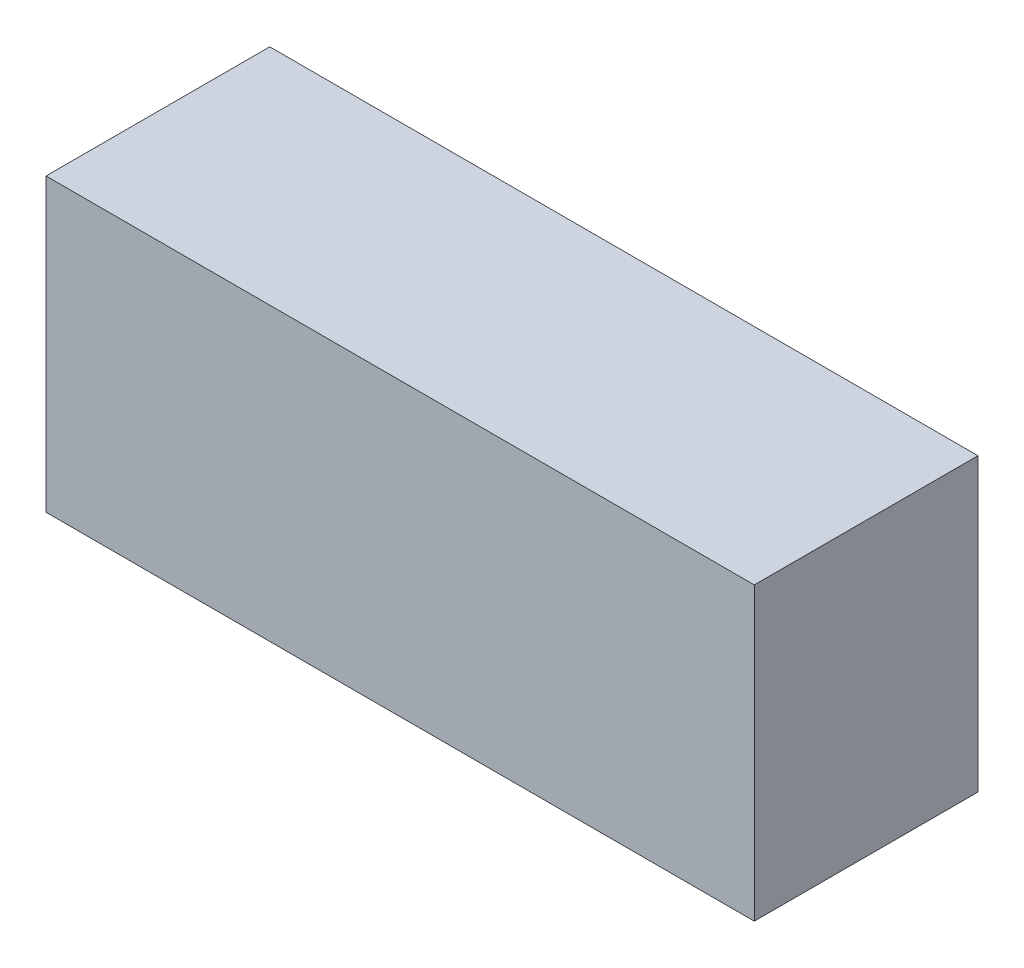
SolidWorks part; units mm, degrees
ref_plane "Front Plane" through (0, 0, 0) normal (0, 0, 1) x (1, 0, 0)
ref_plane "Top Plane" through (0, 0, 0) normal (0, 1, 0) x (1, 0, 0)
ref_plane "Right Plane" through (0, 0, 0) normal (1, 0, 0) x (0, 0, -1)
sketch "Sketch1" plane through (0, 0, 0) normal (0, 1, 0) x (1, 0, 0)
  line L1 (-67.945, 21.463) -> (67.945, 21.463)
  line L2 (-67.945, 21.463) -> (-67.945, -21.463)
  line L3 (-67.945, -21.463) -> (67.945, -21.463)
  line L4 (67.945, 21.463) -> (67.945, -21.463)
  line L5 (-67.945, 21.463) -> (67.945, -21.463) construction
  line L6 (-67.945, -21.463) -> (67.945, 21.463) construction
  point P0 (0, 0)
  dimension "D1" = 135.89
  dimension "D2" = 42.926
extrude "Boss-Extrude1" add sketch "Sketch1" along normal blind 55.88
